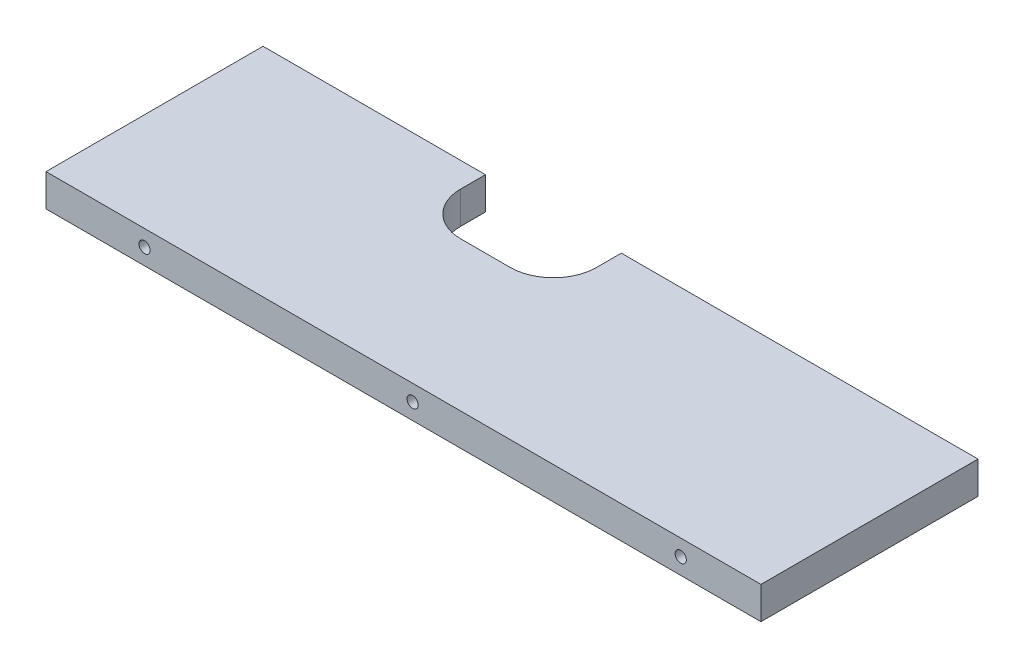
SolidWorks part; units mm, degrees
ref_plane "Front Plane" through (0, 0, 0) normal (0, 0, 1) x (1, 0, 0)
ref_plane "Top Plane" through (0, 0, 0) normal (0, 1, 0) x (1, 0, 0)
ref_plane "Right Plane" through (0, 0, 0) normal (1, 0, 0) x (0, 0, -1)
sketch "Sketch1" plane through (0, 0, 0) normal (0, 0, 1) x (1, 0, 0)
  line L1 (-105.2375, 4.7625) -> (105.2375, 4.7625)
  line L2 (-105.2375, 4.7625) -> (-105.2375, -4.7625)
  line L3 (-105.2375, -4.7625) -> (105.2375, -4.7625)
  line L4 (105.2375, 4.7625) -> (105.2375, -4.7625)
  point P4 (0, 4.7625)
  point P6 (-105.2375, 0)
  dimension "D1" = 210.475
  dimension "D2" = 9.525
extrude "Boss-Extrude1" add sketch "Sketch1" along normal blind 63.9
sketch "Sketch2" plane through (0, 4.7625, 0) normal (0, 1, 0) x (1, 0, 0)
  line L0 (105.2375, 0) -> (-105.2375, 0) construction
  line L1 (-39.7625, 0) -> (0.2375, 0)
  line L2 (-39.7625, 0) -> (-39.7625, -20)
  line L3 (-39.7625, -20) -> (0.2375, -20)
  line L4 (0.2375, 0) -> (0.2375, -20)
  line L5 (105.2375, -63.9) -> (105.2375, 0) construction
  dimension "D1" = 20
  dimension "D2" = 40
  dimension "D3" = 105
extrude "Cut-Extrude1" cut sketch "Sketch2" against normal through all
fillet "Fillet1" radius 12.7 2 edges at (0.2375, 0, 20) (-39.7625, 0, 20)
sketch "Sketch4" plane through (0, 0, 63.9) normal (0, 0, 1) x (1, 0, 0)
  line L0 (105.2375, -4.7625) -> (105.2375, 4.7625) construction
  line L1 (-105.2375, 4.7625) -> (-105.2375, -4.7625) construction
  point P0 (-76.2285, 0)
  point P1 (2.6995, 0)
  point P2 (81.6285, 0)
  point P9 (-105.2375, 0)
  dimension "D1" = 23.609
  dimension "D2" = 78.929
  dimension "D3" = 78.928
hole_wizard "Tap Drill for M4 Tap1" positions "Sketch5" profile "Sketch6" hole size "M4" standard "ISO"
sketch "Sketch5" plane through (0, 0, 63.9) normal (0, 0, 1) x (1, 0, 0)
  point P0 (-76.2285, 0)
  point P3 (2.6995, 0)
  point P6 (81.6285, 0)
sketch "Sketch6" plane through (-76.2285, 0, 63.9) normal (1, 0, 0) x (0, -1, 0)
  line L0 (0, 0) -> (0, 13.6914)
  line L1 (0, 13.6914) -> (1.65, 12.7)
  line L2 (1.65, 12.7) -> (1.65, 0)
  line L5 (1.65, 0) -> (0, 0)
  line L10 (0, 13.6914) -> (-1.65, 12.7) construction
  line L11 (0, -6.35) -> (0, 107.95) construction
  dimension "Hole Dia." = 3.3
  dimension "Hole Depth" = 12.7
  dimension "Drill Angle" = 118
